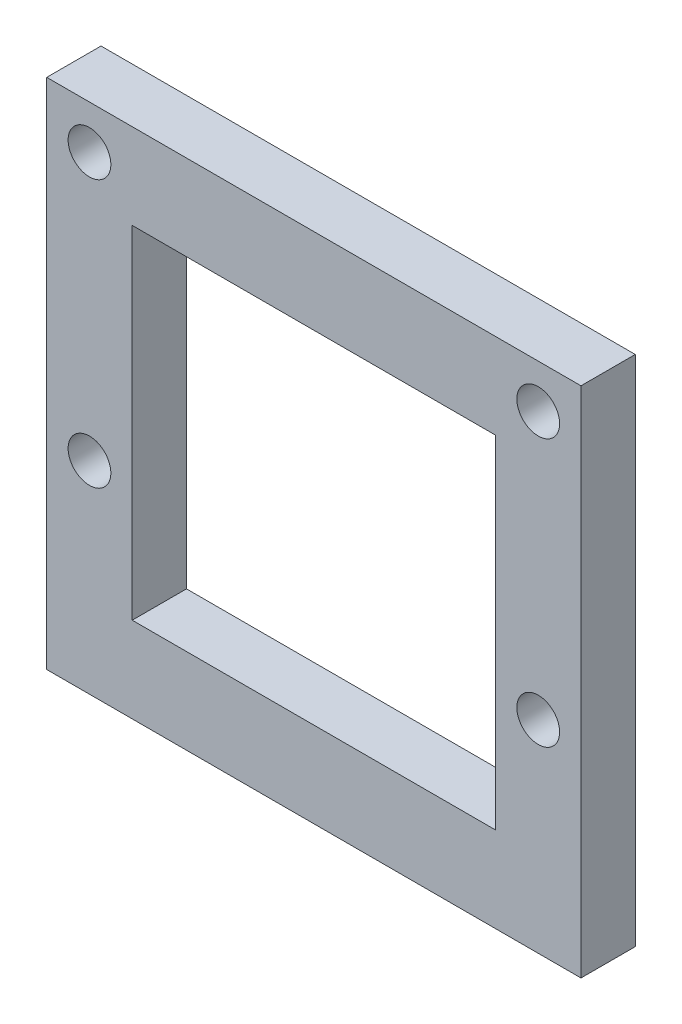
SolidWorks part; units mm, degrees
ref_plane "Front Plane" through (0, 0, 0) normal (0, 0, 1) x (1, 0, 0)
ref_plane "Top Plane" through (0, 0, 0) normal (0, 1, 0) x (1, 0, 0)
ref_plane "Right Plane" through (0, 0, 0) normal (1, 0, 0) x (0, 0, -1)
sketch "Sketch1" plane through (0, 0, 0) normal (0, 0, 1) x (1, 0, 0)
  line L1 (-12.5, 12) -> (12.5, 12)
  line L2 (-12.5, 12) -> (-12.5, -12)
  line L3 (-12.5, -12) -> (12.5, -12)
  line L4 (12.5, 12) -> (12.5, -12)
  line L5 (-12.5, 12) -> (12.5, -12) construction
  line L6 (-12.5, -12) -> (12.5, 12) construction
  line L8 (-8.5, -8) -> (8.5, -8)
  line L9 (-8.5, -8) -> (-8.5, 8)
  line L10 (-8.5, 8) -> (8.5, 8)
  line L11 (8.5, -8) -> (8.5, 8)
  line L12 (-8.5, -8) -> (8.5, 8) construction
  line L13 (-8.5, 8) -> (8.5, -8) construction
  point P0 (0, 0)
  point P8 (0, 0)
  dimension "D1" = 24
  dimension "D2" = 25
  dimension "D3" = 4
  dimension "D4" = 4
extrude "Boss-Extrude1" add sketch "Sketch1" along normal blind 2.54
ref_plane "Plane1" through (0, 0, 0.635) normal (0, 0, 1) x (1, 0, 0)
sketch "Sketch2" plane through (0, 0, 0.635) normal (0, 0, 1) x (1, 0, 0)
  line L0 (-12.5, 12) -> (-12.5, -12) construction
  line L1 (12.5, -12) -> (12.5, 12) construction
  circle A0 centre (-10.5, 9.9634) radius 1
  circle A1 centre (-10.5, -2.5366) radius 1
  circle A2 centre (10.5, 9.9634) radius 1
  circle A3 centre (10.5, -2.5366) radius 1
  dimension "D1" = 2
  dimension "D2" = 2
  dimension "D3" = 12.5
  dimension "D4" = 2
  dimension "D5" = 12.5
extrude "Cut-Extrude1" cut sketch "Sketch2" along normal blind 2.54
